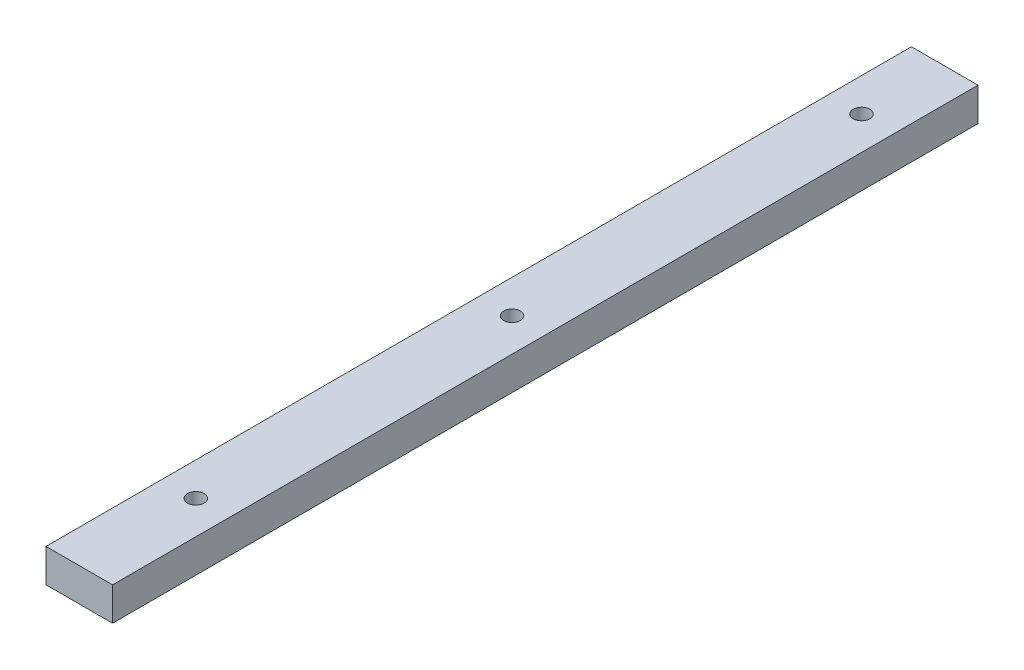
SolidWorks part; units mm, degrees
ref_plane "Front Plane" through (0, 0, 0) normal (0, 0, 1) x (1, 0, 0)
ref_plane "Top Plane" through (0, 0, 0) normal (0, 1, 0) x (1, 0, 0)
ref_plane "Right Plane" through (0, 0, 0) normal (1, 0, 0) x (0, 0, -1)
sketch "Sketch1" plane through (0, 0, 0) normal (0, 0, 1) x (1, 0, 0)
  line L1 (0, 0) -> (50.8, 0)
  line L2 (0, 0) -> (0, 25.4)
  line L3 (0, 25.4) -> (50.8, 25.4)
  line L4 (50.8, 0) -> (50.8, 25.4)
  dimension "D1" = 25.4
  dimension "D2" = 50.8
extrude "Boss-Extrude1" add sketch "Sketch1" along normal blind 660.4
sketch "Sketch2" plane through (0, 25.4, 0) normal (0, 1, 0) x (1, 0, 0)
  line L0 (50.8, 0) -> (0, 0) construction
  line L1 (50.8, -660.4) -> (50.8, 0) construction
  line L2 (50.8, -660.4) -> (0, -660.4) construction
  circle A0 centre (25.4, -63.5) radius 6.35
  circle A1 centre (25.4, -571.5) radius 6.35
  circle A2 centre (25.4, -330.2) radius 6.35
  point P10 (21.0221, -152.2523)
  point P13 (0, 0)
  point P14 (0, 0)
  point P15 (50.8, -330.2)
  dimension "D1" = 12.7
  dimension "D4" = 12.7
  dimension "D7" = 12.7
  dimension "D2" = 63.5
  dimension "D3" = 25.4
  dimension "D5" = 0
  dimension "D6" = 88.9
extrude "Cut-Extrude1" cut sketch "Sketch2" against normal blind 254
